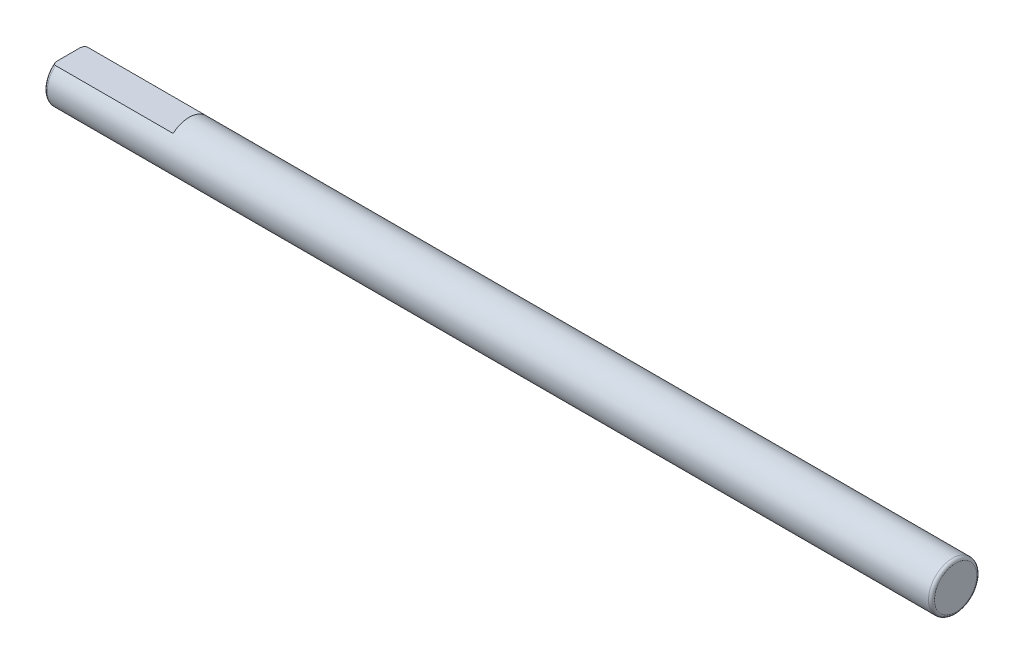
SolidWorks part; units mm, degrees
material "1023 Carbon Steel Sheet (SS)"
ref_plane "Ön Düzlem" through (0, 0, 0) normal (0, 0, 1) x (1, 0, 0)
ref_plane "Üst Düzlem" through (0, 0, 0) normal (0, 1, 0) x (1, 0, 0)
ref_plane "Sağ Düzlem" through (0, 0, 0) normal (1, 0, 0) x (0, 0, -1)
sketch "Sketch1" plane through (0, 0, 0) normal (1, 0, 0) x (0, 0, -1)
  circle A0 centre (0, 0) radius 4
  dimension "D1" = 8
extrude "Boss-Extrude1" add sketch "Sketch1" along normal blind 147
fillet "Fillet1" radius 0.5 2 edges at (147, 0, -4) (0, 0, -4)
sketch "Sketch2" plane through (0, 0, 0) normal (-1, 0, 0) x (0, 0, 1)
  line L1 (-3.0891, 5) -> (3.0891, 5)
  line L2 (-3.0891, 5) -> (-3.0891, 3)
  line L3 (-3.0891, 3) -> (3.0891, 3)
  line L4 (3.0891, 5) -> (3.0891, 3)
  line L5 (-3.0891, 5) -> (3.0891, 3) construction
  line L6 (-3.0891, 3) -> (3.0891, 5) construction
  circle A0 centre (0, 0) radius 4 construction
  point P0 (0, 4)
  dimension "D1" = 2
extrude "Cut-Extrude1" cut sketch "Sketch2" against normal blind 20
